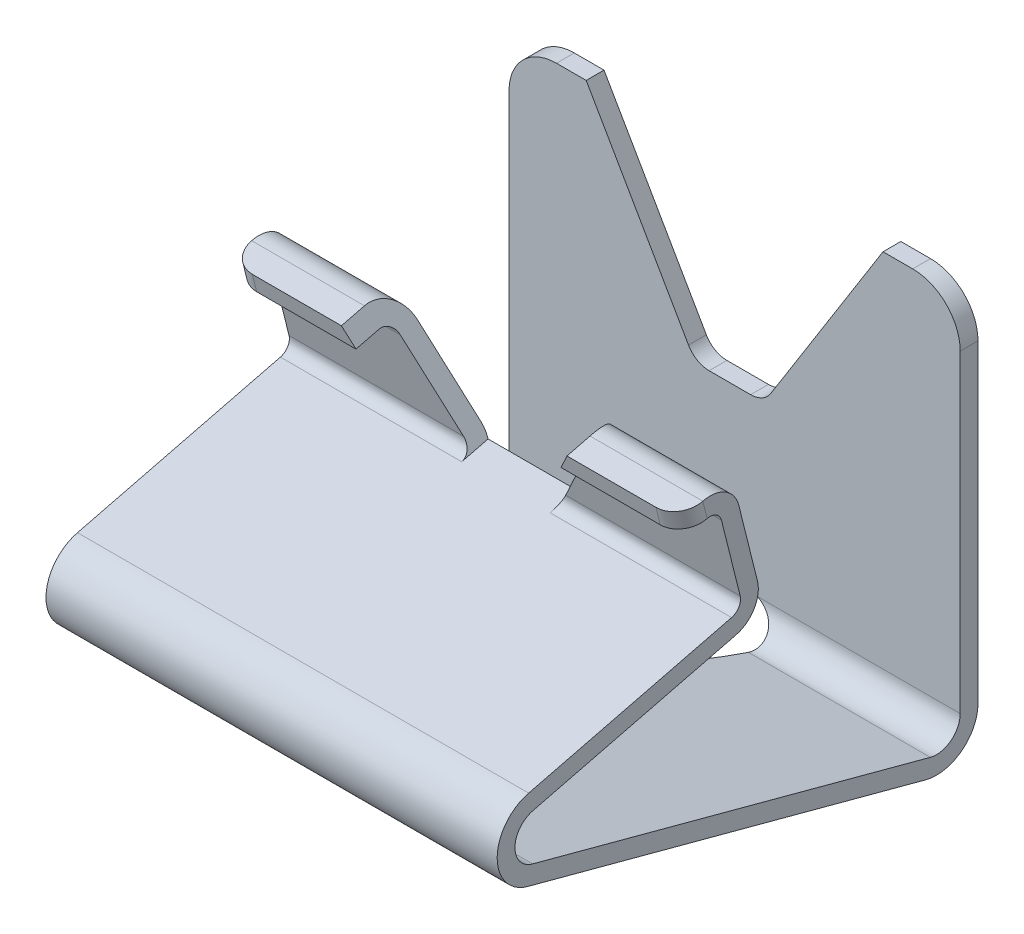
SolidWorks part; units mm, degrees
material "ABS"
ref_plane "Front Plane" through (0, 0, 0) normal (1, 0, 0) x (0, 1, 0)
ref_plane "Top Plane" through (0, 0, 0) normal (0, 0, 1) x (0, 1, 0)
ref_plane "Right Plane" through (0, 0, 0) normal (0, 1, 0) x (-1, 0, 0)
sketch "Sketch1" plane through (0, 0, 0) normal (1, 0, 0) x (0, 1, 0)
  line L0 (9.1226, 0) -> (70, 0)
  line L2 (70, 3) -> (9.1226, 3)
  line L3 (5.2589, 8.0353) -> (23.2115, 75.0355)
  line L4 (30.9564, 74.968) -> (39.4776, 40.7913)
  line L5 (45.5387, 37.1494) -> (58.1526, 40.2944)
  line L6 (61.7944, 46.3555) -> (60.8267, 50.2366)
  line L7 (60.8267, 50.2366) -> (57.9159, 49.5109)
  line L8 (57.9159, 49.5109) -> (58.8835, 45.6297)
  line L9 (57.4268, 43.2053) -> (44.813, 40.0603)
  line L10 (42.3885, 41.517) -> (33.8673, 75.6937)
  line L11 (2.3611, 8.8117) -> (20.3138, 75.812)
  line L12 (70, 3) -> (70, 0)
  arc A2 (23.2115, 75.0355) -> (30.9564, 74.968) centre (27.0752, 74.0003) cw
  arc A3 (33.8673, 75.6937) -> (20.3138, 75.812) centre (27.0752, 74.0003) ccw
  arc A4 (9.1226, 3) -> (5.2589, 8.0353) centre (9.1226, 7) cw
  arc A5 (9.1226, 0) -> (2.3611, 8.8117) centre (9.1226, 7) cw
  arc A6 (58.1526, 40.2944) -> (61.7944, 46.3555) centre (56.943, 45.1459) ccw
  arc A7 (39.4776, 40.7913) -> (45.5387, 37.1494) centre (44.3291, 42.0009) ccw
  arc A8 (58.8835, 45.6297) -> (57.4268, 43.2053) centre (56.943, 45.1459) cw
  arc A9 (44.813, 40.0603) -> (42.3885, 41.517) centre (44.3291, 42.0009) cw
  point P19 (63.004, 41.504)
  point P27 (27.1363, 81)
  point P32 (59.3713, 49.8738)
  point P39 (0, 0)
  dimension "D3" = 4
  dimension "D4" = 7
  dimension "D7" = 3
  dimension "D9" = 81
  dimension "D10" = 23
  dimension "D16" = 4
  dimension "D17" = 7
  dimension "D19" = 5
  dimension "D20" = 2
  dimension "D2" = 3
  dimension "D5" = 75
  dimension "D6" = 3
  dimension "D8" = 29
  dimension "D11" = 90
  dimension "D12" = 3
  dimension "D13" = 47
  dimension "D14" = 3
  dimension "D15" = 9
  dimension "D18" = 70
extrude "Boss-Extrude1" add sketch "Sketch1" along normal mid plane 76
fillet "Fillet1" radius 4 2 edges at (-38, 59.3713, 49.8738) (38, 59.3713, 49.8738)
fillet "Fillet2" radius 8 2 edges at (-38, 70, 1.5) (38, 70, 1.5)
sketch "Sketch2" plane through (0, 0, 0) normal (0, 0, -1) x (1, 0, 0)
  line L0 (-25, -70) -> (-6.6128, -38)
  line L1 (30, -70) -> (-30, -70) construction
  line L2 (-6.6128, -38) -> (4.9122, -38)
  line L3 (4.9122, -38) -> (25, -70)
  line L4 (25, -70) -> (-25, -70)
  line L6 (38, -9.1226) -> (38, -62) construction
  point P5 (0, 0)
  point P10 (-25.113, -15.9095)
  dimension "D1" = 62
  dimension "D2" = 50
  dimension "D3" = 13
  dimension "D4" = 32
extrude "Cut-Extrude1" cut sketch "Sketch2" against normal blind 13 and the other way through all
fillet "Fillet3" radius 4 2 edges at (-6.6128, 38, 1.5) (4.9122, 38, 1.5)
sketch "Sketch4" plane through (0, 0, 0) normal (0, 0, -1) x (1, 0, 0)
  line L0 (38, -2.1226) -> (-38, -2.1226) construction
  circle A0 centre (0, -2.1226) radius 8
  dimension "D1" = 16
extrude "Cut-Extrude4" cut sketch "Sketch4" against normal through all
sketch "Sketch5" plane through (0, -6.7808, 27.1965) normal (0, -0.2419, 0.9703) x (1, 0, 0)
sketch "Sketch6" plane through (0, -6.7808, 27.1965) normal (0, -0.2419, 0.9703) x (1, 0, 0)
  line L0 (-19, 71.1733) -> (-7.453, 51.1733)
  line L1 (-7.453, 51.1733) -> (7.453, 51.1733)
  line L2 (7.453, 51.1733) -> (19, 71.1733)
  line L3 (19, 71.1733) -> (-19, 71.1733)
  line L4 (34, 71.1733) -> (-34, 71.1733) construction
  line L5 (38, 51.1733) -> (-38, 51.1733) construction
  line L6 (38, 66.1733) -> (38, 53.1733) construction
  point P10 (6.854, 51.1733)
  point P11 (0, 51.1733)
  dimension "D1" = 38
  dimension "D2" = 60
  dimension "D3" = 19
extrude "Cut-Extrude5" cut sketch "Sketch6" against normal through all both and the other way through all
